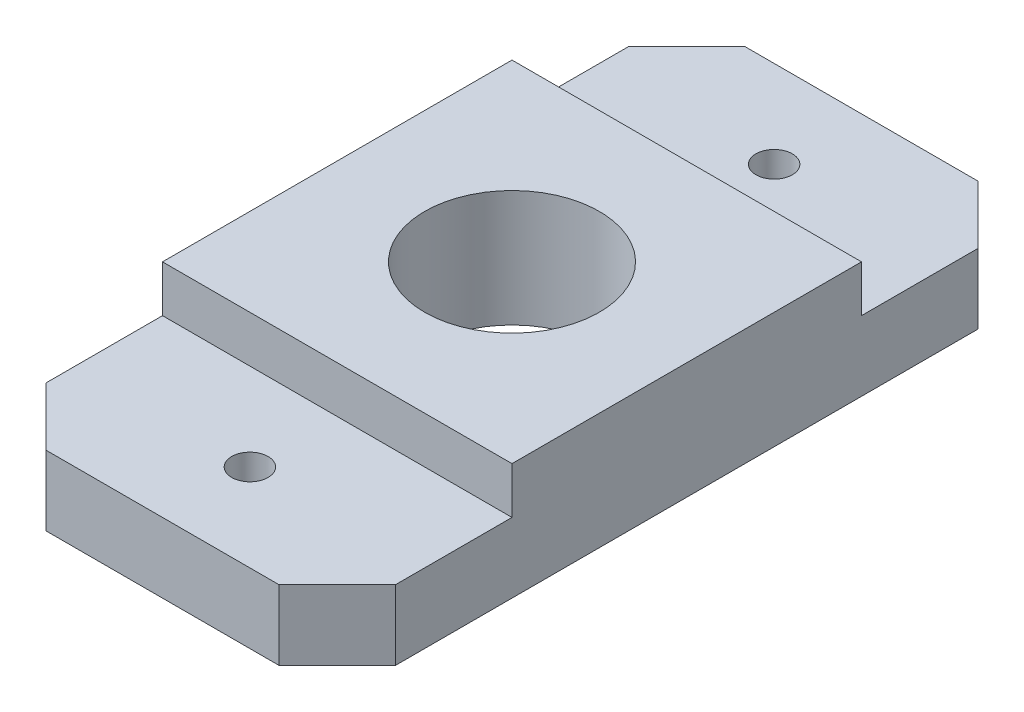
SolidWorks part; units mm, degrees
ref_plane "Front Plane" through (0, 0, 0) normal (0, 0, 1) x (1, 0, 0)
ref_plane "Top Plane" through (0, 0, 0) normal (0, 1, 0) x (1, 0, 0)
ref_plane "Right Plane" through (0, 0, 0) normal (1, 0, 0) x (0, 0, -1)
sketch "Sketch1" plane through (0, 0, 0) normal (0, 1, 0) x (1, 0, 0)
  line L1 (-38.1, -38.1) -> (38.1, -38.1)
  line L2 (-38.1, -38.1) -> (-38.1, 38.1)
  line L3 (-38.1, 38.1) -> (38.1, 38.1)
  line L4 (38.1, -38.1) -> (38.1, 38.1)
  line L5 (0, 38.1) -> (0, -38.1) construction
  line L6 (-38.1, 0) -> (38.1, 0) construction
  point P0 (0, 0)
  dimension "D1" = 76.2
  dimension "D2" = 76.2
extrude "Boss-Extrude1" add sketch "Sketch1" along normal blind 7.62
sketch "Sketch2" plane through (0, 7.62, 0) normal (0, 1, 0) x (1, 0, 0)
  line L1 (-19.05, -19.05) -> (19.05, -19.05)
  line L2 (-19.05, -19.05) -> (-19.05, 19.05)
  line L3 (-19.05, 19.05) -> (19.05, 19.05)
  line L4 (19.05, -19.05) -> (19.05, 19.05)
  line L5 (0, 19.05) -> (0, -19.05) construction
  line L6 (-19.05, 0) -> (19.05, 0) construction
  point P0 (0, 0)
  dimension "D1" = 38.1
  dimension "D2" = 38.1
extrude "Boss-Extrude2" add sketch "Sketch2" along normal blind 5.08 contours L3 L4 L1 L2
sketch "Sketch3" plane through (0, 12.7, 0) normal (0, 1, 0) x (1, 0, 0)
  circle A0 centre (0, 0) radius 9.525
  dimension "D1" = 19.05
extrude "Cut-Extrude1" cut sketch "Sketch3" against normal through all
sketch "Sketch4" plane through (0, 12.7, 0) normal (0, 1, 0) x (1, 0, 0)
  line L1 (38.1, 38.1) -> (-38.1, 38.1) construction
  line L2 (0, 0) -> (40.5468, 0) construction
  circle A0 centre (0, 28.575) radius 1.9844
  circle A1 centre (0, -28.575) radius 1.9844
  dimension "D1" = 3.9688
  dimension "D2" = 9.525
extrude "Cut-Extrude2" cut sketch "Sketch4" against normal through all
sketch "Sketch5" plane through (0, 7.62, 0) normal (0, 1, 0) x (1, 0, 0)
  line L0 (0, -38.1) -> (0, 38.1) construction
  line L1 (-38.1, -38.1) -> (-19.05, -38.1)
  line L2 (-38.1, -38.1) -> (-38.1, 19.05)
  line L4 (-19.05, -38.1) -> (-19.05, 19.05)
  line L5 (-38.1, 38.1) -> (-19.05, 38.1)
  line L6 (-38.1, 38.1) -> (-38.1, 19.05)
  line L8 (-19.05, 38.1) -> (-19.05, 19.05)
  line L9 (19.05, 38.1) -> (19.05, 19.05)
  line L11 (38.1, 38.1) -> (38.1, 19.05)
  line L12 (38.1, 38.1) -> (19.05, 38.1)
  line L13 (19.05, -38.1) -> (19.05, 19.05)
  line L15 (38.1, -38.1) -> (38.1, 19.05)
  line L16 (38.1, -38.1) -> (19.05, -38.1)
extrude "Cut-Extrude3" cut sketch "Sketch5" against normal through all
chamfer "Chamfer1" distance 6.35 4 edges at (19.05, 3.81, -38.1) (-19.05, 3.81, -38.1) (19.05, 3.81, 38.1) (-19.05, 3.81, 38.1)
